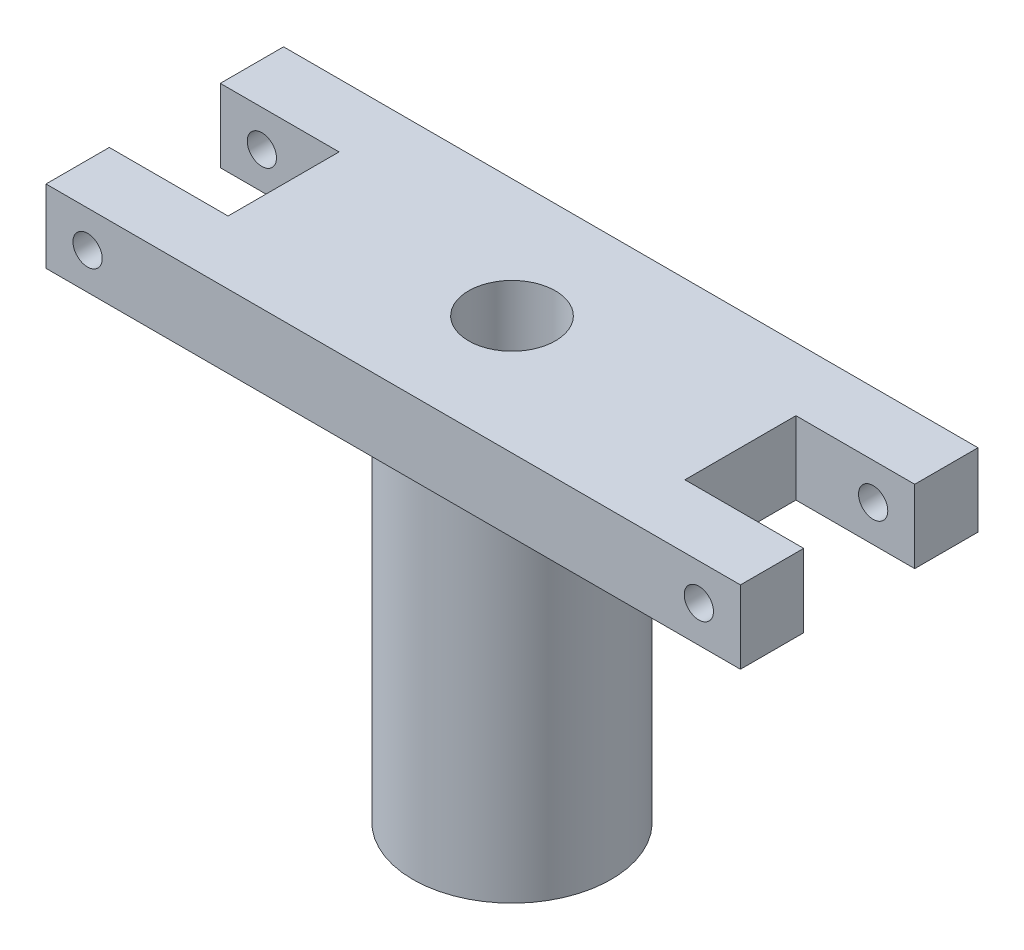
SolidWorks part; units mm, degrees
ref_plane "前视基准面" through (0, 0, 0) normal (0, 0, 1) x (1, 0, 0)
ref_plane "上视基准面" through (0, 0, 0) normal (0, 1, 0) x (1, 0, 0)
ref_plane "右视基准面" through (0, 0, 0) normal (1, 0, 0) x (0, 0, -1)
sketch "草图10" plane through (0, 0, 0) normal (0, 1, 0) x (1, 0, 0)
  circle A0 centre (0, 0) radius 10.85
extrude "凸台-拉伸5" add sketch "草图10" along normal blind 40
sketch "草图11" plane through (0, 0, 0) normal (0, -1, 0) x (-1, 0, 0)
  line L1 (5.74, -4.5426) -> (6.804, 2.6996)
  line L2 (6.804, 2.6996) -> (1.064, 7.2423)
  line L3 (1.064, 7.2423) -> (-5.74, 4.5426)
  line L4 (-5.74, 4.5426) -> (-6.804, -2.6996)
  line L5 (-6.804, -2.6996) -> (-1.064, -7.2423)
  line L6 (-1.064, -7.2423) -> (5.74, -4.5426)
  circle A0 centre (0, 0) radius 6.3393 construction
extrude "切除-拉伸1" cut sketch "草图11" against normal blind 18
sketch "草图12" plane through (0, 40, 0) normal (0, 1, 0) x (1, 0, 0)
  circle A0 centre (0, 0) radius 4.75
extrude "切除-拉伸2" cut sketch "草图12" against normal blind 18
sketch "草图13" plane through (0, 22, 0) normal (0, 1, 0) x (1, 0, 0)
  circle A0 centre (0, 0) radius 2.1
extrude "切除-拉伸3" cut sketch "草图13" against normal blind 4
sketch "草图14" plane through (0, 40, 0) normal (0, 1, 0) x (1, 0, 0)
  line L1 (38, -13) -> (-38, -13)
  line L2 (38, -13) -> (38, 13)
  line L3 (38, 13) -> (-38, 13)
  line L4 (-38, -13) -> (-38, 13)
  line L5 (0, 13) -> (0, -13) construction
  line L6 (38, 0) -> (-38, 0) construction
  point P0 (0, 0)
extrude "凸台-拉伸8" add sketch "草图14" along normal blind 8
sketch "草图15" plane through (0, 48, 0) normal (0, 1, 0) x (1, 0, 0)
  circle A0 centre (0, 0) radius 4.75
extrude "切除-拉伸4" cut sketch "草图15" against normal blind 8
sketch "草图16" plane through (0, 0, 13) normal (0, 0, 1) x (1, 0, 0)
  circle A0 centre (-33.45, 44) radius 1.6
  circle A1 centre (33.45, 44) radius 1.6
extrude "切除-拉伸5" cut sketch "草图16" against normal blind 26
sketch "草图17" plane through (0, 40, 0) normal (0, -1, 0) x (1, 0, 0)
  line L0 (38, 13) -> (38, -13) construction
  line L1 (25, 6.075) -> (38, 6.075)
  line L2 (25, 6.075) -> (25, -6.075)
  line L3 (25, -6.075) -> (38, -6.075)
  line L4 (38, 6.075) -> (38, -6.075)
  line L5 (-38, -13) -> (-38, 13) construction
  line L6 (-25, -6.075) -> (-38, -6.075)
  line L7 (-25, -6.075) -> (-25, 6.075)
  line L8 (-25, 6.075) -> (-38, 6.075)
  line L9 (-38, -6.075) -> (-38, 6.075)
extrude "切除-拉伸6" cut sketch "草图17" against normal blind 8
